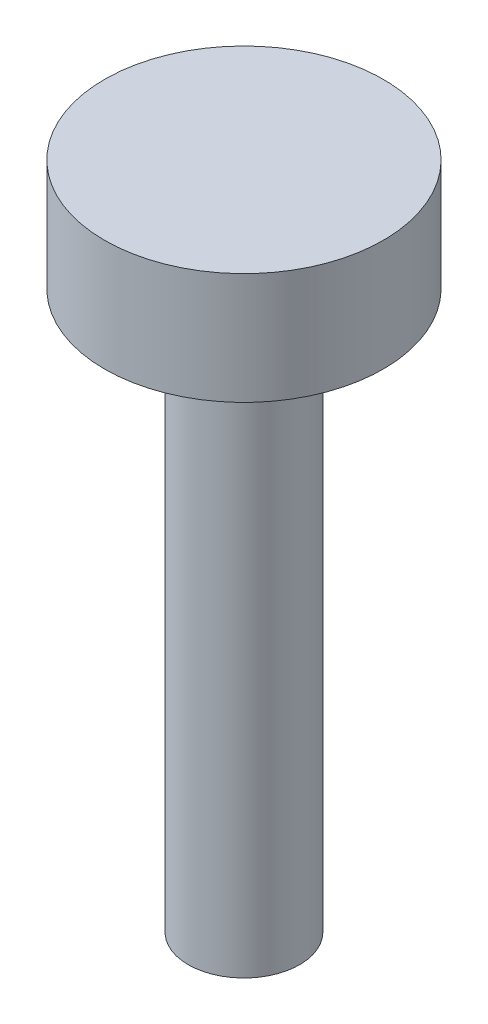
SolidWorks part; units mm, degrees
ref_plane "Front Plane" through (0, 0, 0) normal (0, 0, 1) x (1, 0, 0)
ref_plane "Top Plane" through (0, 0, 0) normal (0, 1, 0) x (1, 0, 0)
ref_plane "Right Plane" through (0, 0, 0) normal (1, 0, 0) x (0, 0, -1)
sketch "Sketch4" plane through (0, 0, 0) normal (0, 1, 0) x (1, 0, 0)
  circle A0 centre (0, 0) radius 10
  dimension "D1" = 20
extrude "Boss-Extrude5" add sketch "Sketch4" along normal blind 100
sketch "Sketch5" plane through (0, 100, 0) normal (0, 1, 0) x (1, 0, 0)
  circle A0 centre (0, 0) radius 25
  dimension "D1" = 50
extrude "Boss-Extrude6" add sketch "Sketch5" along normal blind 20
